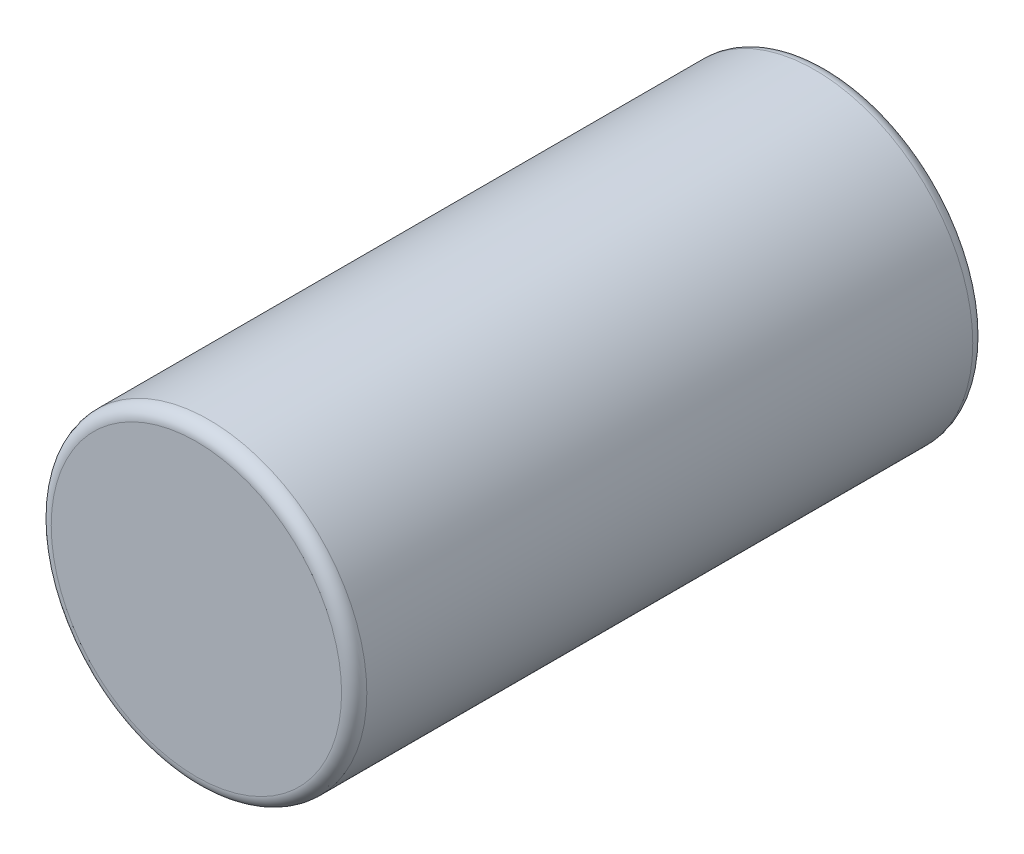
SolidWorks part; units mm, degrees
material "Plain Carbon Steel"
ref_plane "Front" through (0, 0, 0) normal (0, 0, 1) x (1, 0, 0)
ref_plane "Top" through (0, 0, 0) normal (0, 1, 0) x (1, 0, 0)
ref_plane "Right" through (0, 0, 0) normal (1, 0, 0) x (0, 0, -1)
sketch "Sketch1" plane through (0, 0, 0) normal (0, 0, 1) x (1, 0, 0)
  circle A0 centre (0, 0) radius 3.175
  dimension "D1" = 6.35
extrude "Boss-Extrude1" add sketch "Sketch1" along normal blind 12.7
fillet "Fillet1" radius 0.254 2 edges at (3.175, 0, 0) (3.175, 0, 12.7)
